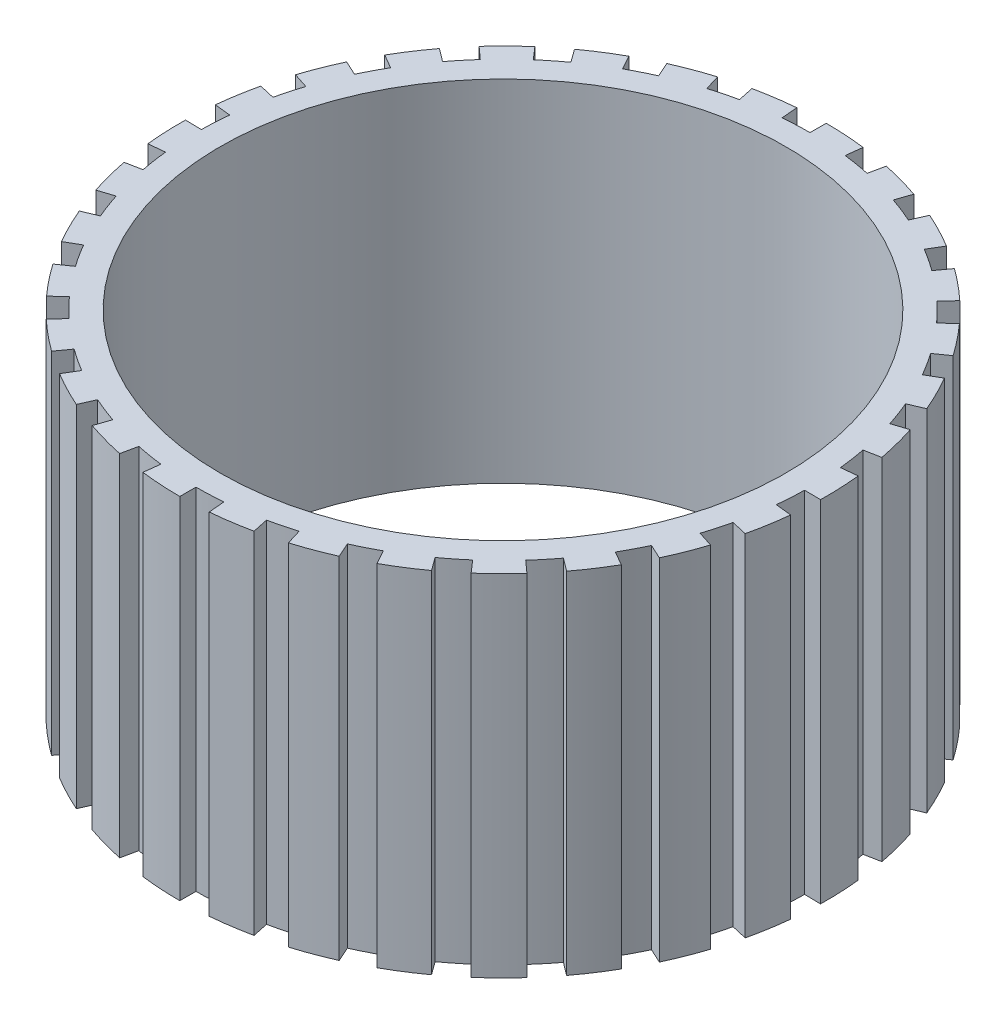
SolidWorks part; units mm, degrees
ref_plane "Front Plane" through (0, 0, 0) normal (0, 0, 1) x (1, 0, 0)
ref_plane "Top Plane" through (0, 0, 0) normal (0, 1, 0) x (1, 0, 0)
ref_plane "Right Plane" through (0, 0, 0) normal (1, 0, 0) x (0, 0, -1)
sketch "Sketch1" plane through (0, 0, 0) normal (0, 1, 0) x (1, 0, 0)
  line L0 (0, 57) -> (0, 60)
  line L1 (6.9466, 56.5751) -> (7.3122, 59.5528)
  line L2 (11.851, 55.7544) -> (12.4747, 58.6889)
  line L3 (18.5574, 53.8946) -> (19.5341, 56.7311)
  line L4 (23.184, 52.0721) -> (24.4042, 54.8127)
  line L5 (29.3572, 48.8585) -> (30.9023, 51.43)
  line L6 (33.5038, 46.114) -> (35.2671, 48.541)
  line L7 (38.8739, 41.6872) -> (40.9199, 43.8812)
  line L8 (42.3593, 38.1404) -> (44.5887, 40.1478)
  line L9 (46.6917, 32.6939) -> (49.1491, 34.4146)
  line L10 (49.3634, 28.5) -> (51.9615, 30)
  line L11 (52.4688, 22.2717) -> (55.2303, 23.4439)
  line L12 (54.2102, 17.614) -> (57.0634, 18.541)
  line L13 (55.9527, 10.8761) -> (58.8976, 11.4485)
  line L14 (56.6877, 5.9581) -> (59.6713, 6.2717)
  line L15 (56.9913, -0.9948) -> (59.9909, -1.0471)
  line L16 (56.6877, -5.9581) -> (59.6713, -6.2717)
  line L17 (55.5391, -12.8222) -> (58.4622, -13.4971)
  line L18 (54.2102, -17.614) -> (57.0634, -18.541)
  line L19 (51.6595, -24.0892) -> (54.3785, -25.3571)
  line L20 (49.3634, -28.5) -> (51.9615, -30)
  line L21 (45.5222, -34.3035) -> (47.9181, -36.1089)
  line L22 (42.3593, -38.1404) -> (44.5887, -40.1478)
  line L23 (37.3954, -43.0184) -> (39.3635, -45.2826)
  line L24 (33.5038, -46.114) -> (35.2671, -48.541)
  line L25 (27.6341, -49.8533) -> (29.0886, -52.4772)
  line L26 (23.184, -52.0721) -> (24.4042, -54.8127)
  line L27 (16.6652, -54.5094) -> (17.5423, -57.3783)
  line L28 (11.851, -55.7544) -> (12.4747, -58.6889)
  line L29 (4.9679, -56.7831) -> (5.2293, -59.7717)
  line L30 (0, -57) -> (0, -60)
  line L31 (-6.9466, -56.5751) -> (-7.3122, -59.5528)
  line L32 (-11.851, -55.7544) -> (-12.4747, -58.6889)
  line L33 (-18.5574, -53.8946) -> (-19.5341, -56.7311)
  line L34 (-23.184, -52.0721) -> (-24.4042, -54.8127)
  line L35 (-29.3572, -48.8585) -> (-30.9023, -51.43)
  line L36 (-33.5038, -46.114) -> (-35.2671, -48.541)
  line L37 (-38.8739, -41.6872) -> (-40.9199, -43.8812)
  line L38 (-42.3593, -38.1404) -> (-44.5887, -40.1478)
  line L39 (-46.6917, -32.6939) -> (-49.1491, -34.4146)
  line L40 (-49.3634, -28.5) -> (-51.9615, -30)
  line L41 (-52.4688, -22.2717) -> (-55.2303, -23.4439)
  line L42 (-54.2102, -17.614) -> (-57.0634, -18.541)
  line L43 (-55.9527, -10.8761) -> (-58.8976, -11.4485)
  line L44 (-56.6877, -5.9581) -> (-59.6713, -6.2717)
  line L45 (-56.9913, 0.9948) -> (-59.9909, 1.0471)
  line L46 (-56.6877, 5.9581) -> (-59.6713, 6.2717)
  line L47 (-55.5391, 12.8222) -> (-58.4622, 13.4971)
  line L48 (-54.2102, 17.614) -> (-57.0634, 18.541)
  line L49 (-51.6595, 24.0892) -> (-54.3785, 25.3571)
  line L50 (-49.3634, 28.5) -> (-51.9615, 30)
  line L51 (-45.5222, 34.3035) -> (-47.9181, 36.1089)
  line L52 (-42.3593, 38.1404) -> (-44.5887, 40.1478)
  line L53 (-37.3954, 43.0184) -> (-39.3635, 45.2826)
  line L54 (-33.5038, 46.114) -> (-35.2671, 48.541)
  line L55 (-27.6341, 49.8533) -> (-29.0886, 52.4772)
  line L56 (-23.184, 52.0721) -> (-24.4042, 54.8127)
  line L57 (-16.6652, 54.5094) -> (-17.5423, 57.3783)
  line L58 (-11.851, 55.7544) -> (-12.4747, 58.6889)
  line L59 (-4.9679, 56.7831) -> (-5.2293, 59.7717)
  circle A0 centre (0, 0) radius 52.5
  arc A1 (7.3122, 59.5528) -> (0, 60) centre (0, 0) ccw
  arc A2 (11.851, 55.7544) -> (6.9466, 56.5751) centre (0, 0) ccw
  arc A3 (19.5341, 56.7311) -> (12.4747, 58.6889) centre (0, 0) ccw
  arc A4 (23.184, 52.0721) -> (18.5574, 53.8946) centre (0, 0) ccw
  arc A5 (30.9023, 51.43) -> (24.4042, 54.8127) centre (0, 0) ccw
  arc A6 (33.5038, 46.114) -> (29.3572, 48.8585) centre (0, 0) ccw
  arc A7 (40.9199, 43.8812) -> (35.2671, 48.541) centre (0, 0) ccw
  arc A8 (42.3593, 38.1404) -> (38.8739, 41.6872) centre (0, 0) ccw
  arc A9 (49.1491, 34.4146) -> (44.5887, 40.1478) centre (0, 0) ccw
  arc A10 (49.3634, 28.5) -> (46.6917, 32.6939) centre (0, 0) ccw
  arc A11 (55.2303, 23.4439) -> (51.9615, 30) centre (0, 0) ccw
  arc A12 (54.2102, 17.614) -> (52.4688, 22.2717) centre (0, 0) ccw
  arc A13 (58.8976, 11.4485) -> (57.0634, 18.541) centre (0, 0) ccw
  arc A14 (56.6877, 5.9581) -> (55.9527, 10.8761) centre (0, 0) ccw
  arc A15 (59.9909, -1.0471) -> (59.6713, 6.2717) centre (0, 0) ccw
  arc A16 (56.6877, -5.9581) -> (56.9913, -0.9948) centre (0, 0) ccw
  arc A17 (58.4622, -13.4971) -> (59.6713, -6.2717) centre (0, 0) ccw
  arc A18 (54.2102, -17.614) -> (55.5391, -12.8222) centre (0, 0) ccw
  arc A19 (54.3785, -25.3571) -> (57.0634, -18.541) centre (0, 0) ccw
  arc A20 (49.3634, -28.5) -> (51.6595, -24.0892) centre (0, 0) ccw
  arc A21 (47.9181, -36.1089) -> (51.9615, -30) centre (0, 0) ccw
  arc A22 (42.3593, -38.1404) -> (45.5222, -34.3035) centre (0, 0) ccw
  arc A23 (39.3635, -45.2826) -> (44.5887, -40.1478) centre (0, 0) ccw
  arc A24 (33.5038, -46.114) -> (37.3954, -43.0184) centre (0, 0) ccw
  arc A25 (29.0886, -52.4772) -> (35.2671, -48.541) centre (0, 0) ccw
  arc A26 (23.184, -52.0721) -> (27.6341, -49.8533) centre (0, 0) ccw
  arc A27 (17.5423, -57.3783) -> (24.4042, -54.8127) centre (0, 0) ccw
  arc A28 (11.851, -55.7544) -> (16.6652, -54.5094) centre (0, 0) ccw
  arc A29 (5.2293, -59.7717) -> (12.4747, -58.6889) centre (0, 0) ccw
  arc A30 (0, -57) -> (4.9679, -56.7831) centre (0, 0) ccw
  arc A31 (-7.3122, -59.5528) -> (0, -60) centre (0, 0) ccw
  arc A32 (-11.851, -55.7544) -> (-6.9466, -56.5751) centre (0, 0) ccw
  arc A33 (-19.5341, -56.7311) -> (-12.4747, -58.6889) centre (0, 0) ccw
  arc A34 (-23.184, -52.0721) -> (-18.5574, -53.8946) centre (0, 0) ccw
  arc A35 (-30.9023, -51.43) -> (-24.4042, -54.8127) centre (0, 0) ccw
  arc A36 (-33.5038, -46.114) -> (-29.3572, -48.8585) centre (0, 0) ccw
  arc A37 (-40.9199, -43.8812) -> (-35.2671, -48.541) centre (0, 0) ccw
  arc A38 (-42.3593, -38.1404) -> (-38.8739, -41.6872) centre (0, 0) ccw
  arc A39 (-49.1491, -34.4146) -> (-44.5887, -40.1478) centre (0, 0) ccw
  arc A40 (-49.3634, -28.5) -> (-46.6917, -32.6939) centre (0, 0) ccw
  arc A41 (-55.2303, -23.4439) -> (-51.9615, -30) centre (0, 0) ccw
  arc A42 (-54.2102, -17.614) -> (-52.4688, -22.2717) centre (0, 0) ccw
  arc A43 (-58.8976, -11.4485) -> (-57.0634, -18.541) centre (0, 0) ccw
  arc A44 (-56.6877, -5.9581) -> (-55.9527, -10.8761) centre (0, 0) ccw
  arc A45 (-59.9909, 1.0471) -> (-59.6713, -6.2717) centre (0, 0) ccw
  arc A46 (-56.6877, 5.9581) -> (-56.9913, 0.9948) centre (0, 0) ccw
  arc A47 (-58.4622, 13.4971) -> (-59.6713, 6.2717) centre (0, 0) ccw
  arc A48 (-54.2102, 17.614) -> (-55.5391, 12.8222) centre (0, 0) ccw
  arc A49 (-54.3785, 25.3571) -> (-57.0634, 18.541) centre (0, 0) ccw
  arc A50 (-49.3634, 28.5) -> (-51.6595, 24.0892) centre (0, 0) ccw
  arc A51 (-47.9181, 36.1089) -> (-51.9615, 30) centre (0, 0) ccw
  arc A52 (-42.3593, 38.1404) -> (-45.5222, 34.3035) centre (0, 0) ccw
  arc A53 (-39.3635, 45.2826) -> (-44.5887, 40.1478) centre (0, 0) ccw
  arc A54 (-33.5038, 46.114) -> (-37.3954, 43.0184) centre (0, 0) ccw
  arc A55 (-29.0886, 52.4772) -> (-35.2671, 48.541) centre (0, 0) ccw
  arc A56 (-23.184, 52.0721) -> (-27.6341, 49.8533) centre (0, 0) ccw
  arc A57 (-17.5423, 57.3783) -> (-24.4042, 54.8127) centre (0, 0) ccw
  arc A58 (-11.851, 55.7544) -> (-16.6652, 54.5094) centre (0, 0) ccw
  arc A59 (-5.2293, 59.7717) -> (-12.4747, 58.6889) centre (0, 0) ccw
  arc A60 (0, 57) -> (-4.9679, 56.7831) centre (0, 0) ccw
  point P156 (0, 0)
  dimension "D1" = 105
  dimension "D2" = 120
  dimension "D3" = 114
  dimension "D4" = 7
  dimension "D5" = 7
  dimension "D6" = 5
  dimension "D7" = 57
  dimension "D8" = 30
extrude "Boss-Extrude1" add sketch "Sketch1" along normal blind 65 contours L0 A60 L59 A59 L58 A58 L57 A57 L56 A56 L55 A55 L54 A54 L53 A53 L52 A52 L51 A51 L50 A50 L49 A49 L48 A48 L47 A47 L46 A46 L45 A45 L44 A44 L43 A43 L42 A42 L41 A41 L40 A40 L39 A39 L38 A38 L37 A37 L36 A36 L35
